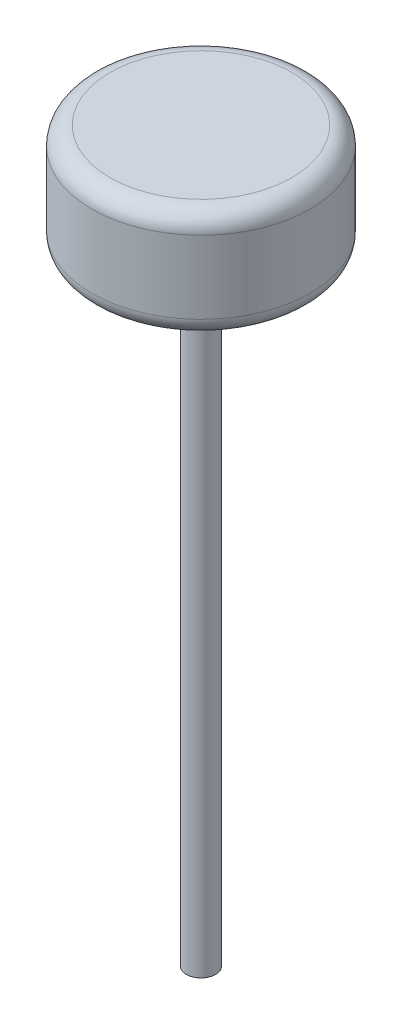
SolidWorks part; units mm, degrees
ref_plane "Front Plane" through (0, 0, 0) normal (0, 0, 1) x (1, 0, 0)
ref_plane "Top Plane" through (0, 0, 0) normal (0, 1, 0) x (1, 0, 0)
ref_plane "Right Plane" through (0, 0, 0) normal (1, 0, 0) x (0, 0, -1)
sketch "Sketch1" plane through (0, 0, 0) normal (0, 1, 0) x (1, 0, 0)
  circle A0 centre (0, 0) radius 4
  dimension "D1" = 8
extrude "Boss-Extrude1" add sketch "Sketch1" along normal blind 170
sketch "Sketch2" plane through (0, 170, 0) normal (0, 1, 0) x (1, 0, 0)
  circle A0 centre (0, 0) radius 30
  dimension "D1" = 60
extrude "Boss-Extrude2" add sketch "Sketch2" along normal blind 30
fillet "Fillet1" radius 5 2 edges at (0, 170, 30) (0, 200, 30)
